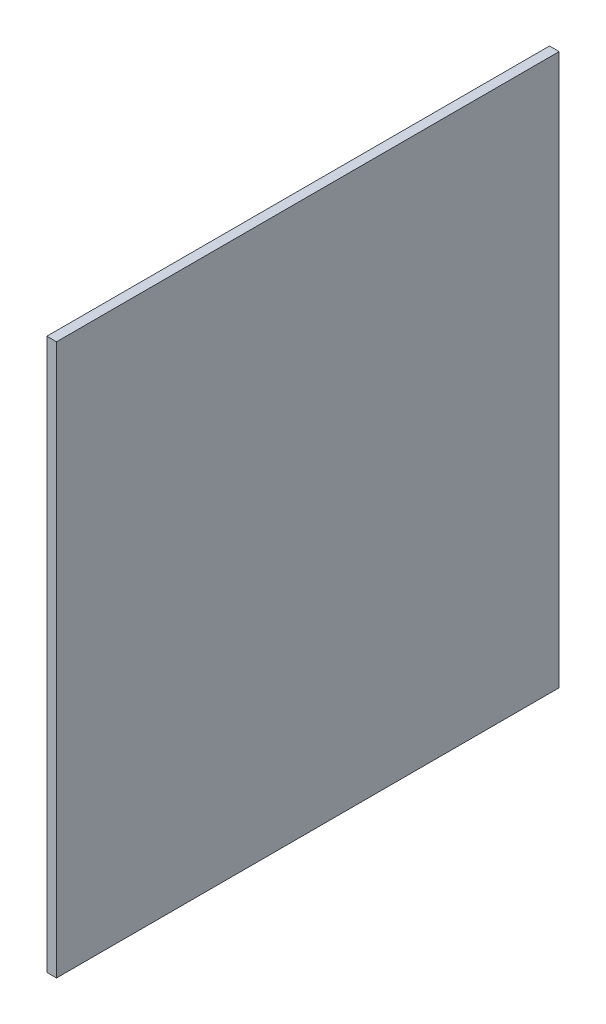
SolidWorks part; units mm, degrees
ref_plane "Plan de face" through (0, 0, 0) normal (0, 0, 1) x (1, 0, 0)
ref_plane "Plan de dessus" through (0, 0, 0) normal (0, 1, 0) x (1, 0, 0)
ref_plane "Plan de droite" through (0, 0, 0) normal (1, 0, 0) x (0, 0, -1)
sketch "Esquisse1" plane through (0, 0, 0) normal (1, 0, 0) x (0, 0, -1)
  line L1 (-406.8773, 232.1283) -> (113.1227, 232.1283)
  line L2 (-406.8773, 232.1283) -> (-406.8773, -337.8717)
  line L3 (-406.8773, -337.8717) -> (113.1227, -337.8717)
  line L4 (113.1227, 232.1283) -> (113.1227, -337.8717)
  dimension "D1" = 570
  dimension "D2" = 520
extrude "Boss.-Extru.1" add sketch "Esquisse1" along normal blind 10
equation "\"HauteurPlacard\" = 550"
equation "\"D1@Esquisse1\" = \"HauteurPlacard\" + 2 * \"EpaisseurPlaque\""
equation "\"LargeurPlacard\"=360"
equation "\"ProfondeurPlacard\"=520"
equation "\"EpaisseurPlaque\"= 10"
equation "\"D2@Esquisse1\"=\"ProfondeurPlacard\""
equation "\"D1@Boss.-Extru.1\"=\"EpaisseurPlaque\""
